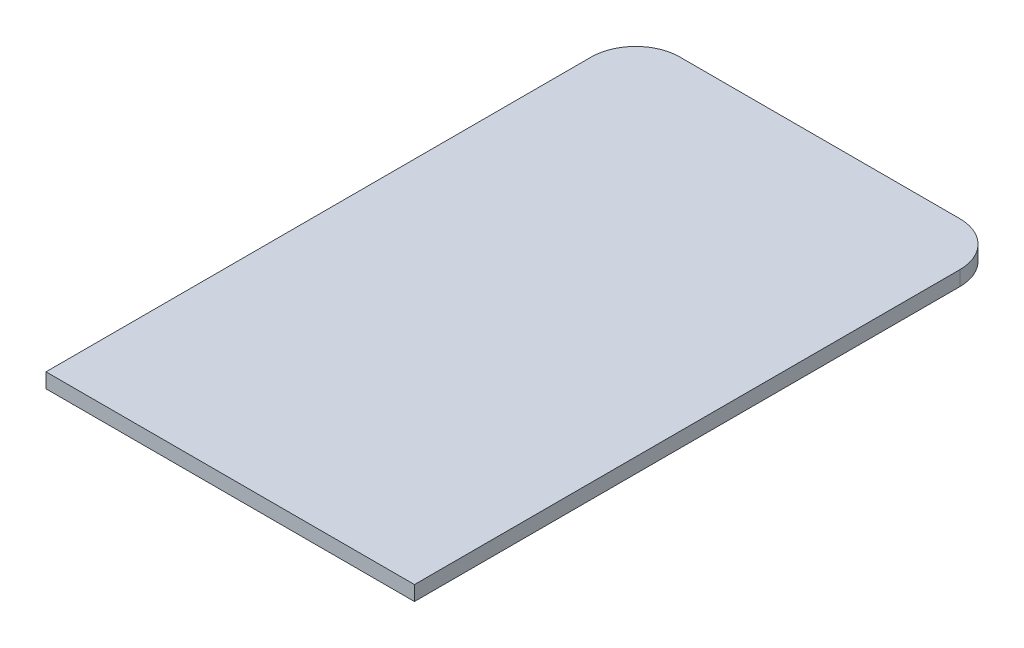
SolidWorks part; units mm, degrees
ref_plane "Front Plane" through (0, 0, 0) normal (0, 0, 1) x (1, 0, 0)
ref_plane "Top Plane" through (0, 0, 0) normal (0, 1, 0) x (1, 0, 0)
ref_plane "Right Plane" through (0, 0, 0) normal (1, 0, 0) x (0, 0, -1)
sketch "Sketch1" plane through (0, 0, 0) normal (0, 1, 0) x (1, 0, 0)
  line L0 (0, 0) -> (1.25, 0)
  line L1 (1.25, 0) -> (1.25, 3.7)
  line L2 (0.95, 4) -> (-0.95, 4)
  line L3 (-1.25, 3.7) -> (-1.25, 0)
  line L4 (-1.25, 0) -> (0, 0)
  arc A0 (1.25, 3.7) -> (0.95, 4) centre (0.95, 3.7) ccw
  arc A1 (-0.95, 4) -> (-1.25, 3.7) centre (-0.95, 3.7) ccw
  point P8 (1.25, 4)
  point P11 (-1.25, 4)
  dimension "D3" = 0.3
  dimension "D1" = 4
  dimension "D2" = 2.5
extrude "Boss-Extrude1" add sketch "Sketch1" along normal blind 0.1
